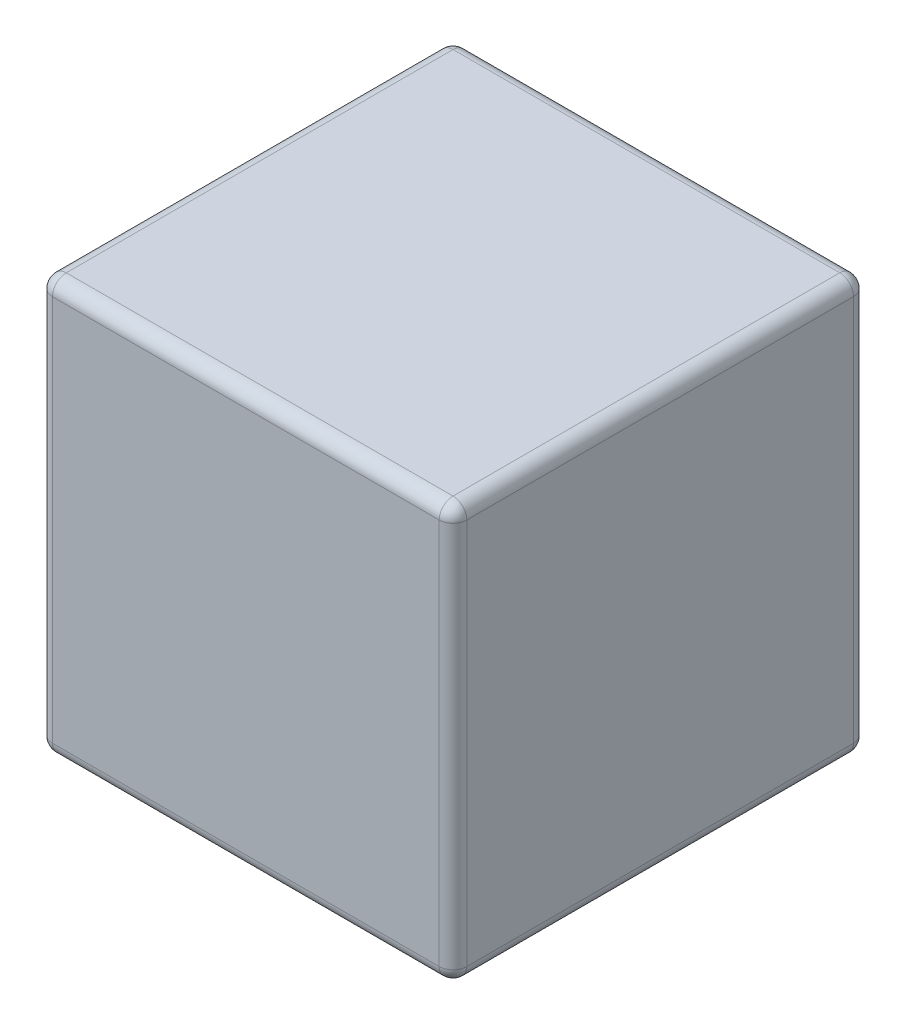
SolidWorks part; units mm, degrees
material "Plain Carbon Steel"
ref_plane "Front Plane" through (0, 0, 0) normal (1, 0, 0) x (0, 1, 0)
ref_plane "Top Plane" through (0, 0, 0) normal (0, 0, 1) x (0, 1, 0)
ref_plane "Right Plane" through (0, 0, 0) normal (0, 1, 0) x (-1, 0, 0)
sketch "Sketch1" plane through (0, 0, 0) normal (1, 0, 0) x (0, 1, 0)
  line L1 (0, 0) -> (3, 0)
  line L2 (0, 0) -> (0, 3)
  line L3 (0, 3) -> (3, 3)
  line L4 (3, 0) -> (3, 3)
  dimension "D1" = 3
  dimension "D2" = 3
extrude "Boss-Extrude1" add sketch "Sketch1" along normal mid plane 3
fillet "Fillet1" radius 0.1 12 edges at (-1.5, 0, 1.5) (0, 0, 0) (-1.5, 1.5, 0) (0, 0, 3) (-1.5, 1.5, 3) (1.5, 1.5, 3) (1.5, 1.5, 0) (1.5, 0, 1.5) (0, 3, 0) (1.5, 3, 1.5) (0, 3, 3) (-1.5, 3, 1.5)
